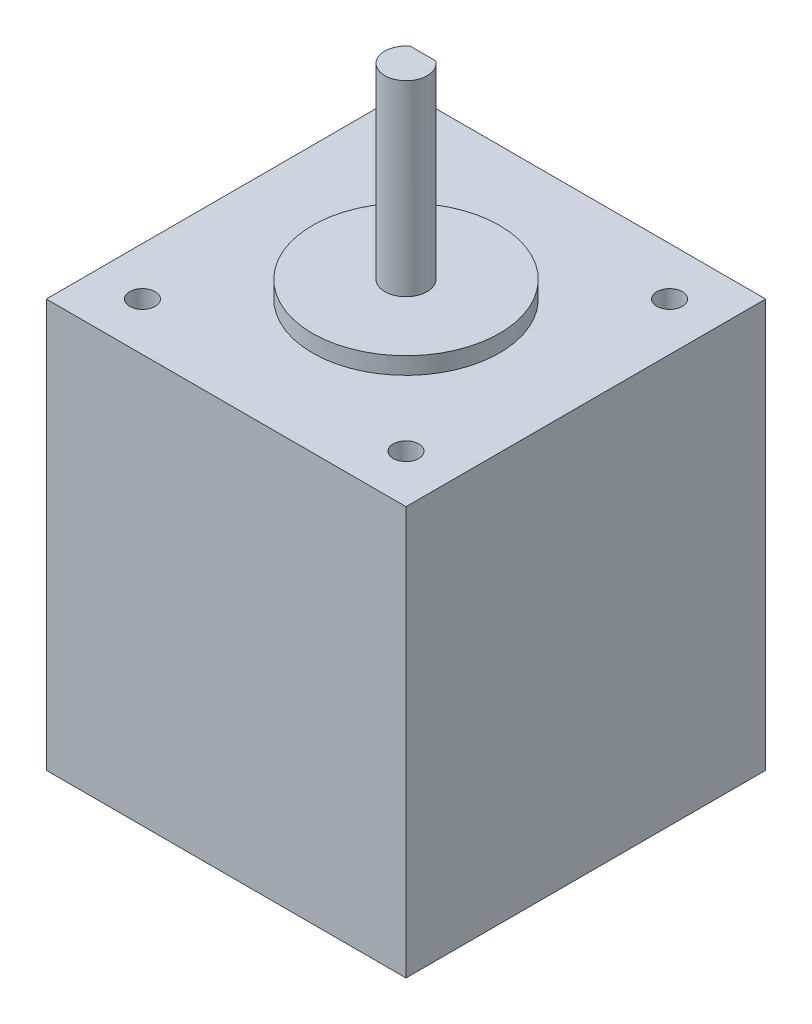
SolidWorks part; units mm, degrees
ref_plane "Front Plane" through (0, 0, 0) normal (0, 0, 1) x (1, 0, 0)
ref_plane "Top Plane" through (0, 0, 0) normal (0, 1, 0) x (1, 0, 0)
ref_plane "Right Plane" through (0, 0, 0) normal (1, 0, 0) x (0, 0, -1)
sketch "Sketch1" plane through (0, 0, 0) normal (0, 1, 0) x (1, 0, 0)
  line L1 (-21.15, 21.15) -> (21.15, 21.15)
  line L2 (-21.15, 21.15) -> (-21.15, -21.15)
  line L3 (-21.15, -21.15) -> (21.15, -21.15)
  line L4 (21.15, 21.15) -> (21.15, -21.15)
  line L5 (-21.15, 21.15) -> (21.15, -21.15) construction
  line L6 (-21.15, -21.15) -> (21.15, 21.15) construction
  point P0 (0, 0)
  dimension "D1" = 42.3
extrude "Boss-Extrude1" add sketch "Sketch1" along normal blind 48
sketch "Sketch2" plane through (0, 48, 0) normal (0, 1, 0) x (1, 0, 0)
  circle A0 centre (0, 0) radius 11
  dimension "D1" = 22
extrude "Boss-Extrude2" add sketch "Sketch2" along normal blind 2
sketch "Sketch3" plane through (0, 48, 0) normal (0, 1, 0) x (1, 0, 0)
  circle A0 centre (0, 0) radius 2.5
  dimension "D1" = 5
extrude "Boss-Extrude3" add sketch "Sketch3" along normal blind 24
sketch "Sketch4" plane through (0, 48, 0) normal (0, 1, 0) x (1, 0, 0)
  line L0 (0, 21.15) -> (0, 0) construction
  line L1 (21.15, 21.15) -> (-21.15, 21.15) construction
  line L2 (0, 0) -> (21.15, 0) construction
  line L3 (21.15, -21.15) -> (21.15, 21.15) construction
  circle A0 centre (15.5, 15.5) radius 1.5
  circle A1 centre (15.5, -15.5) radius 1.5
  circle A2 centre (-15.5, 15.5) radius 1.5
  circle A3 centre (-15.5, -15.5) radius 1.5
  dimension "D3" = 3
  dimension "D1" = 31
  dimension "D2" = 31
extrude "Cut-Extrude1" cut sketch "Sketch4" against normal blind 4
sketch "Sketch5" plane through (0, 72, 0) normal (0, 1, 0) x (1, 0, 0)
  line L0 (-1.5, 2) -> (1.5, 2)
  circle A0 centre (0, 0) radius 2.5 construction
  circle A1 centre (0, 0) radius 2.5 construction
  circle A2 centre (0, 0) radius 2.5
  point P6 (0, -2.5)
  circle M3 centre (0, 0) radius 2.5
  dimension "D1" = 4.5
extrude "Cut-Extrude2" cut sketch "Sketch5" against normal blind 20 contours L0 M3
